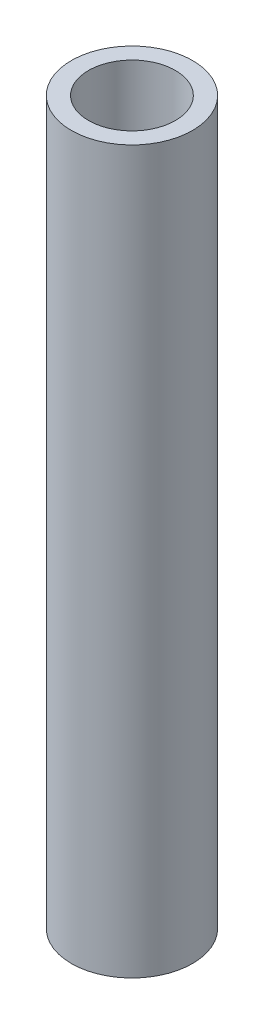
SolidWorks part; units mm, degrees
ref_plane "Front Plane" through (0, 0, 0) normal (0, 0, 1) x (1, 0, 0)
ref_plane "Top Plane" through (0, 0, 0) normal (0, 1, 0) x (1, 0, 0)
ref_plane "Right Plane" through (0, 0, 0) normal (1, 0, 0) x (0, 0, -1)
sketch "Sketch1" plane through (0, 0, 0) normal (0, 1, 0) x (1, 0, 0)
  circle A0 centre (0, 0) radius 10.668
  circle A1 centre (0, 0) radius 7.6454
  dimension "D1" = 21.336
  dimension "D2" = 15.2908
extrude "Boss-Extrude1" add sketch "Sketch1" along normal blind 127
ref_plane "Plane1" through (0, 63.5, 0) normal (0, -1, 0) x (-1, 0, 0)
